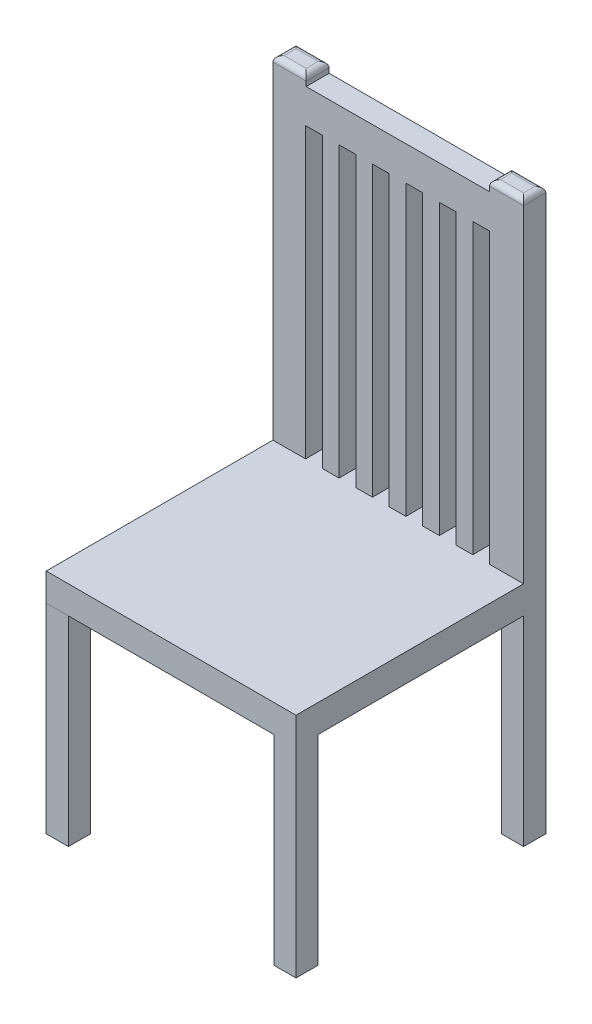
SolidWorks part; units mm, degrees
ref_plane "Front Plane" through (0, 0, 0) normal (0, 0, 1) x (1, 0, 0)
ref_plane "Top Plane" through (0, 0, 0) normal (0, 1, 0) x (1, 0, 0)
ref_plane "Right Plane" through (0, 0, 0) normal (1, 0, 0) x (0, 0, -1)
sketch "Sketch1" plane through (0, 0, 0) normal (0, 1, 0) x (1, 0, 0)
  line L2 (-225, 225) -> (225, 225)
  line L3 (225, 225) -> (225, -225)
  line L4 (225, -225) -> (-225, -225)
  line L5 (-225, -225) -> (-225, 225)
  point P6 (0, 0)
  point P9 (0, 225)
extrude "Boss-Extrude1" add sketch "Sketch1" along normal blind 50
sketch "Sketch2" plane through (0, 0, 0) normal (0, -1, 0) x (-1, 0, 0)
  line L0 (225, -225) -> (185, -225.0043)
  line L1 (185, -225.0043) -> (185, -185.0043)
  line L2 (185, -185.0043) -> (225, -185.0022)
  line L5 (185.0009, 225) -> (185, 185)
  line L8 (-225, 225) -> (-185, 225)
  line L9 (-185, 225) -> (-185, 185)
  line L10 (-185, 185) -> (-225, 185)
  line L11 (-225, 185) -> (-225, 225)
  line L12 (-225, -225) -> (-185, -225)
  line L13 (-185, -225) -> (-185, -185)
  line L14 (-185, -185) -> (-225, -185)
  line L15 (-225, -185) -> (-225, -225)
  line L18 (185, 185) -> (225, 185)
  line L19 (225, 185) -> (225, 225)
  line L20 (225, 225) -> (185.0009, 225)
  line L21 (225, -185.0022) -> (225, -225)
  dimension "D1" = 40
  dimension "D2" = 40
  dimension "D3" = 40
  dimension "D5" = 40
  dimension "D6" = 40
  dimension "D7" = 40
  dimension "D8" = 40
  dimension "D9" = 40
  dimension "D10" = 40
  dimension "D12" = 40
extrude "Boss-Extrude2" add sketch "Sketch2" along normal blind 360
sketch "Sketch3" plane through (0, 50, 0) normal (0, 1, 0) x (1, 0, 0)
  line L0 (-225, 225) -> (-225, 183.3195)
  line L1 (-225, 183.3195) -> (225, 185)
  line L2 (225, 185) -> (225, 225)
  line L3 (225, 225) -> (-225, 225)
  point P9 (0, 184.1598)
extrude "Boss-Extrude3" add sketch "Sketch3" along normal blind 600
sketch "Sketch4" plane through (-0.6877, 0, -184.1572) normal (0.0037, 0, 1) x (1, 0, -0.0037)
  line L0 (-165.5, 50) -> (-165.5, 570)
  line L1 (-165.5, 50) -> (-135.5, 50)
  line L2 (74.5, 50) -> (104.5, 50)
  line L3 (-105.5, 50) -> (-75.5, 50)
  line L4 (-224.3139, 650) -> (225.6893, 650) construction
  line L5 (-45.5, 50) -> (-15.5, 50)
  line L6 (134.5, 50) -> (164.5, 50)
  line L7 (14.5, 50) -> (44.5, 50)
  line L8 (-165.5, 570) -> (-135.5, 570)
  line L9 (-135.5, 570) -> (-135.5, 50)
  line L10 (-105.5, 50) -> (-105.5, 570)
  line L11 (-105.5, 570) -> (-75.5, 570)
  line L12 (-75.5, 570) -> (-75.5, 50)
  line L13 (-45.5, 50) -> (-45.5, 570)
  line L14 (-45.5, 570) -> (-15.5, 570)
  line L15 (-15.5, 570) -> (-15.5, 50)
  line L16 (14.5, 50) -> (14.5, 570)
  line L17 (14.5, 570) -> (44.5, 570)
  line L18 (44.5, 570) -> (44.5, 50)
  line L19 (74.5, 50) -> (74.5, 570)
  line L20 (74.5, 570) -> (104.5, 570)
  line L21 (104.5, 570) -> (104.5, 50)
  line L22 (134.5, 50) -> (134.5, 570)
  line L23 (134.5, 570) -> (164.5, 570)
  line L24 (164.5, 570) -> (164.5, 50)
  line L27 (-164.5, 631.4325) -> (164.5, 631.4325)
  line L28 (164.5, 631.4325) -> (164.5, 652.5154)
  line L29 (164.5, 652.5154) -> (-164.5, 650)
  line L30 (-164.5, 650) -> (-164.5, 631.4325)
  point P29 (0, 631.4325)
  dimension "D1" = 30
  dimension "D2" = 30
  dimension "D3" = 30
  dimension "D4" = 30
  dimension "D5" = 30
  dimension "D6" = 30
  dimension "D7" = 30
  dimension "D8" = 30
  dimension "D9" = 30
  dimension "D10" = 30
  dimension "D11" = 30
  dimension "D12" = 80
extrude "Cut-Extrude2" cut sketch "Sketch4" against normal mid plane 600
fillet "Fillet2" radius 10 4 edges at (194.4056, 650, -184.8857) (225, 650, -205) (194.3305, 650, -225) (163.736, 650, -204.8857)
fillet "Fillet4" radius 10 4 edges at (-195.1707, 650, -225) (-225, 650, -204.1598) (-195.0933, 650, -183.4312) (-165.264, 650, -204.2714)
